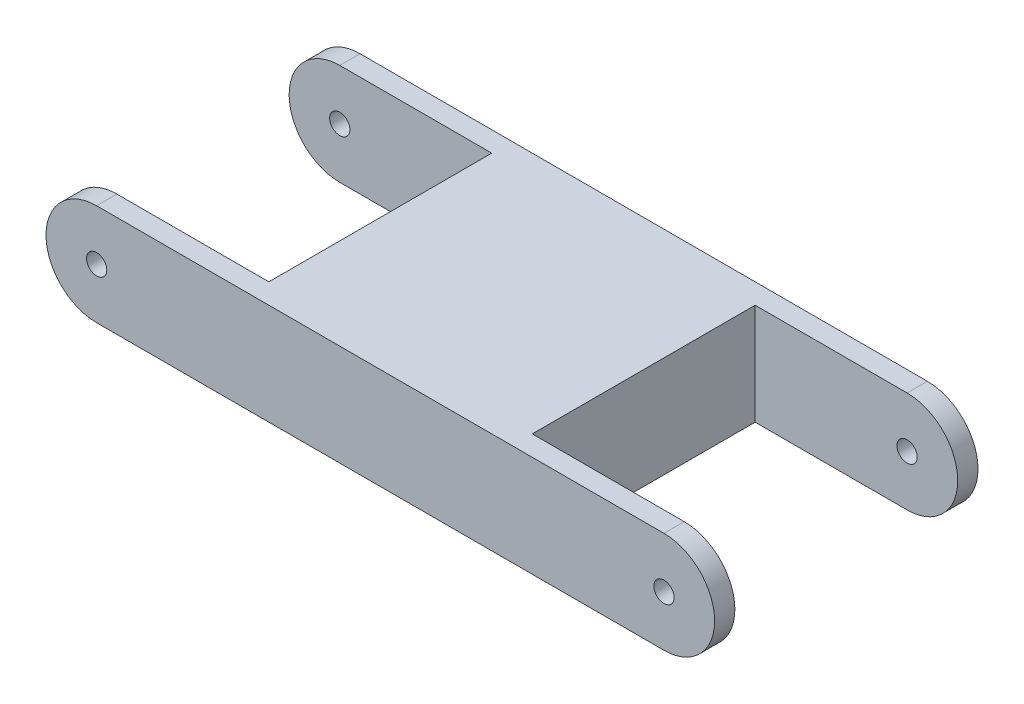
SolidWorks part; units mm, degrees
ref_plane "前基準面" through (0, 0, 0) normal (0, 0, 1) x (1, 0, 0)
ref_plane "上基準面" through (0, 0, 0) normal (0, 1, 0) x (1, 0, 0)
ref_plane "右基準面" through (0, 0, 0) normal (1, 0, 0) x (0, 0, -1)
sketch "草圖1" plane through (0, 0, 0) normal (0, 0, 1) x (1, 0, 0)
  line L0 (0, 47.1991) -> (0, -46.8309) construction
  line L1 (-71.1827, 0) -> (68.2665, 0) construction
  line L2 (-28, 0) -> (28, 0) construction
  line L3 (-28, 5) -> (28, 5)
  line L4 (-28, -5) -> (28, -5)
  arc A0 (-28, 5) -> (-28, -5) centre (-28, 0) ccw
  arc A1 (28, -5) -> (28, 5) centre (28, 0) ccw
  point P7 (0, 0)
  dimension "D2" = 5
  dimension "D1" = 56
extrude "填料-伸長1" add sketch "草圖1" along normal blind 26
sketch "草圖2" plane through (0, 0, 0) normal (0, 0, 1) x (1, 0, 0)
  line L0 (-45.1846, 0) -> (43.8227, 0) construction
  line L1 (0, 28.0802) -> (0, -27.5995) construction
  circle A0 centre (-28, 0) radius 1
  circle A1 centre (28, 0) radius 1
  dimension "D1" = 2
extrude "除料-伸長4" cut sketch "草圖2" against normal blind 30 and the other way through all
sketch "草圖3" plane through (0, 0, 0) normal (0, 1, 0) x (1, 0, 0)
  line L0 (28, 0) -> (-28, 0) construction
  line L1 (-33, -2) -> (-13, -2)
  line L2 (-33, -2) -> (-33, -24)
  line L3 (-33, -24) -> (-13, -24)
  line L4 (-13, -2) -> (-13, -24)
  line L5 (-28, -26) -> (-28, 0) construction
  line L6 (0, 16.8532) -> (0, -37.2241) construction
  line L7 (13, -2) -> (13, -24)
  line L8 (33, -24) -> (13, -24)
  line L9 (33, -2) -> (33, -24)
  line L10 (33, -2) -> (13, -2)
  dimension "D1" = 20
  dimension "D2" = 22
  dimension "D3" = 2
  dimension "D4" = 15
extrude "除料-伸長5" cut sketch "草圖3" against normal blind 30 and the other way blind 30
